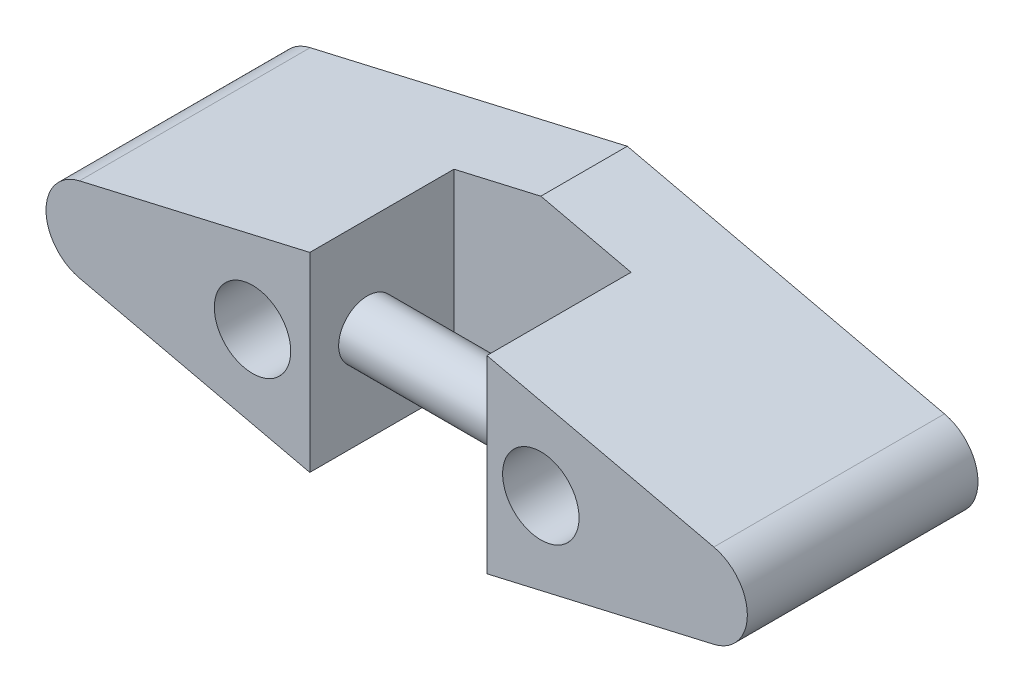
SolidWorks part; units mm, degrees
material "ABS"
ref_plane "Front Plane" through (0, 0, 0) normal (0, 0, 1) x (1, 0, 0)
ref_plane "Top Plane" through (0, 0, 0) normal (0, 1, 0) x (1, 0, 0)
ref_plane "Right Plane" through (0, 0, 0) normal (1, 0, 0) x (0, 0, -1)
sketch "Sketch1" plane through (0, 0, 0) normal (0, 0, 1) x (1, 0, 0)
  line L0 (0, 8) -> (0, -8) construction
  line L1 (0, 8) -> (-22, 2.9225)
  line L2 (-21.9998, -2.9238) -> (0, -8)
  line L3 (21.9998, -2.9238) -> (0, -8)
  line L4 (0, 8) -> (22, 2.9225)
  circle A0 centre (10, 0) radius 2.65
  circle A1 centre (-10, 0) radius 2.65
  arc A2 (-22, 2.9225) -> (-21.9998, -2.9238) centre (-21.3254, -0.0006) ccw
  arc A3 (22, 2.9225) -> (21.9998, -2.9238) centre (21.3254, -0.0006) cw
  point P4 (0, 0)
  point P9 (0, 0)
  point P11 (0, 0)
  dimension "D2" = 5.3
  dimension "D3" = 5.3
  dimension "D5" = 3
  dimension "D1" = 10
  dimension "D4" = 10
extrude "Boss-Extrude1" add sketch "Sketch1" along normal blind 16
sketch "Sketch3" plane through (0, 0, 16) normal (0, 0, 1) x (1, 0, 0)
  line L1 (-6.026, 13.0867) -> (6.2578, 13.0867)
  line L2 (-6.026, 13.0867) -> (-6.026, -8)
  line L3 (-6.026, -8) -> (6.2578, -8)
  line L4 (6.2578, 13.0867) -> (6.2578, -8)
extrude "Cut-Extrude2" cut sketch "Sketch3" against normal blind 10 contours L2 L3 L4 L1
sketch "Sketch4" plane through (6.2578, 0, 0) normal (-1, 0, 0) x (0, 0, 1)
  line L0 (16, 6.5557) -> (6, 6.5557) construction
  line L1 (6, 6.5557) -> (6, -6.5561) construction
  circle A0 centre (12, 0.0007) radius 2
  dimension "D1" = 4
  dimension "D2" = 6.555
  dimension "D3" = 6
extrude "Boss-Extrude2" add sketch "Sketch4" along normal up to next
